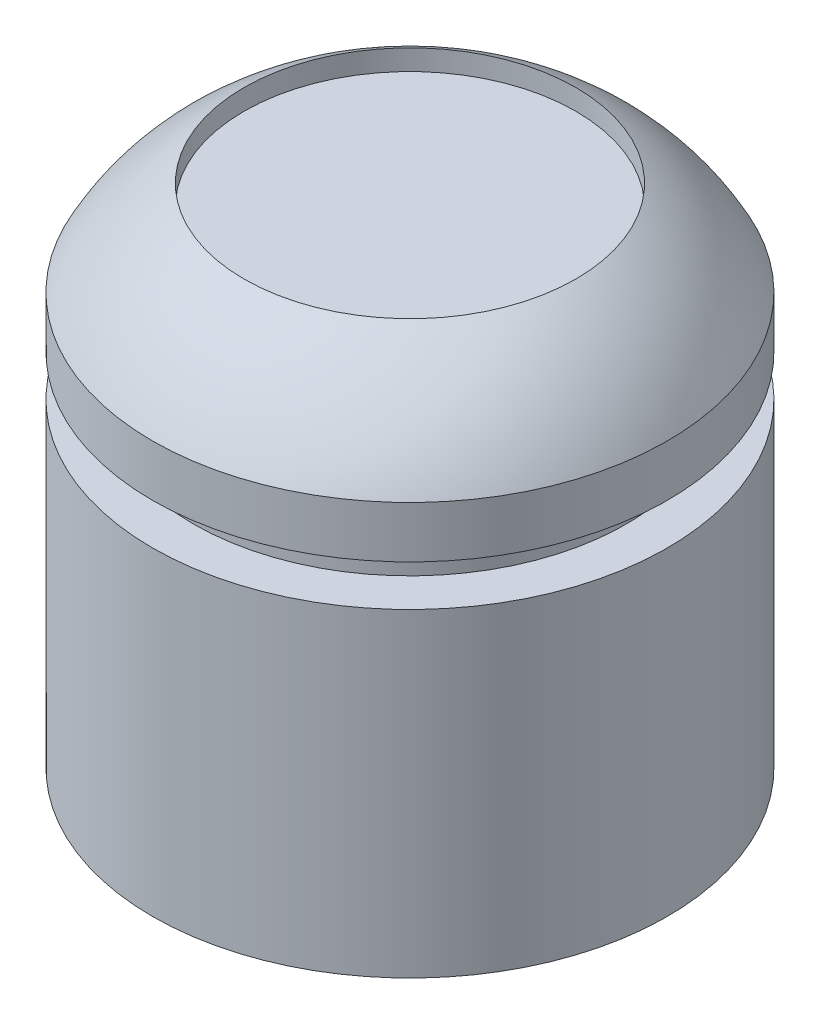
SolidWorks part; units mm, degrees
ref_plane "Front Plane" through (0, 0, 0) normal (0, 0, 1) x (1, 0, 0)
ref_plane "Top Plane" through (0, 0, 0) normal (0, 1, 0) x (1, 0, 0)
ref_plane "Right Plane" through (0, 0, 0) normal (1, 0, 0) x (0, 0, -1)
sketch "Sketch1" plane through (0, 0, 0) normal (1, 0, 0) x (0, 0, -1)
  line L0 (0, 0) -> (0, 15.5)
  line L1 (12.5, 25.7844) -> (12.5, -1.739) construction
  line L2 (4.4429, 24.5882) -> (12.5, 24.5882)
  line L3 (0, 17.5) -> (2, 17.5)
  line L4 (2, 17.5) -> (2, 15.5)
  line L5 (2, 15.5) -> (0, 15.5)
  line L6 (0, 17.5) -> (0, 20)
  line L7 (0, 0) -> (12.5, 0)
  line L8 (12.5, 24.5882) -> (12.5, 0)
  spline S0 degree 2 poles (0, 20) (1.5561, 22.9612) (4.4429, 24.5882) knots 0 0 0 1 1 1
  dimension "D1" = 20
  dimension "D2" = 12.5
  dimension "D3" = 2
  dimension "D4" = 2
  dimension "D5" = 2.5
revolve "Revolve2" add sketch "Sketch1" angle 360 about L8
sketch "Sketch2" plane through (0, 0, 0) normal (0, -1, 0) x (1, 0, 0)
  circle A0 centre (0, -12.5) radius 1.5
  circle A1 centre (0, -12.5) radius 12.5 construction
  dimension "D1" = 11
extrude "Cut-Extrude1" cut sketch "Sketch2" against normal blind 4
sketch "Sketch3" plane through (0, 24.5882, 0) normal (0, 1, 0) x (1, 0, 0)
  circle A0 centre (0, 12.5) radius 8.0571
extrude "Cut-Extrude2" cut sketch "Sketch3" against normal blind 1
